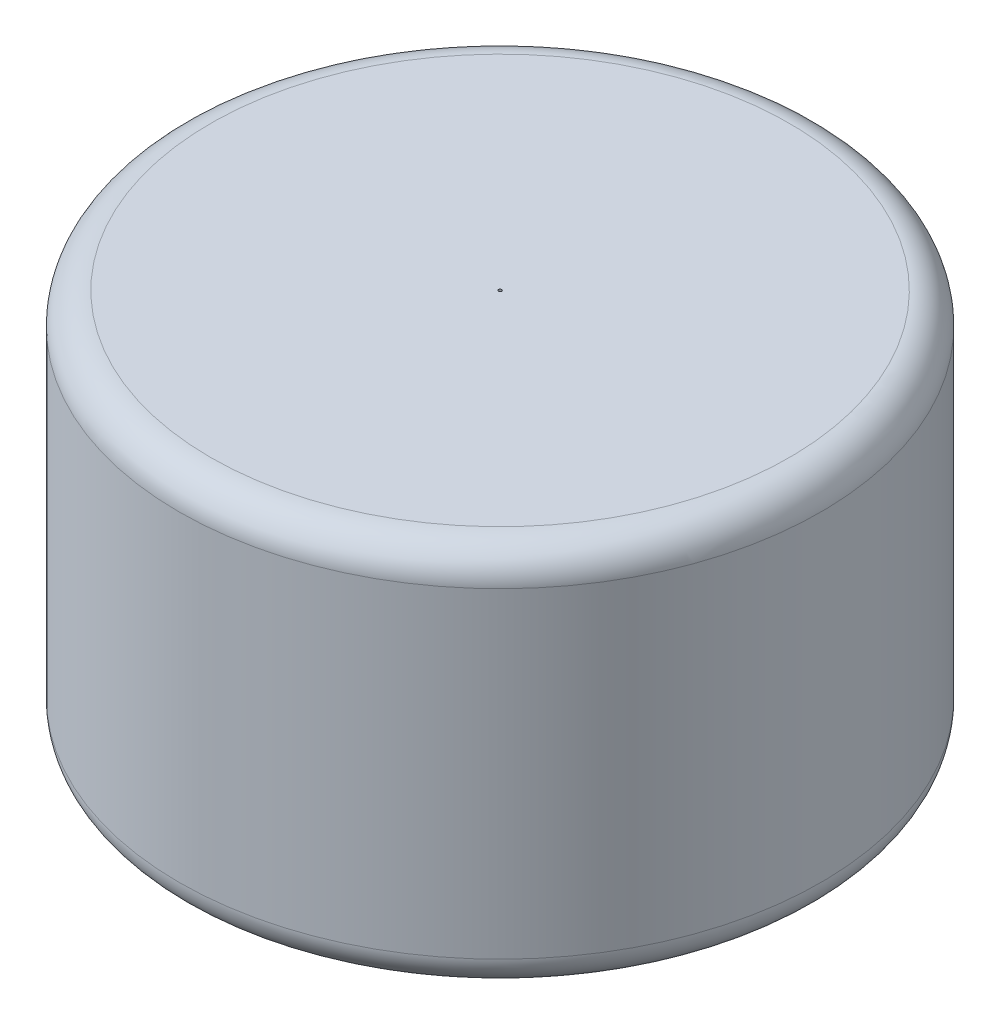
SolidWorks part; units mm, degrees
other "相机1"
other "相机2"
material "PEN"
ref_plane "前视基准面" through (0, 0, 0) normal (0, 0, 1) x (1, 0, 0)
ref_plane "上视基准面" through (0, 0, 0) normal (0, 1, 0) x (1, 0, 0)
ref_plane "右视基准面" through (0, 0, 0) normal (1, 0, 0) x (0, 0, -1)
sketch "草图1" plane through (0, 0, 0) normal (0, 1, 0) x (1, 0, 0)
  circle A0 centre (0, 0) radius 51
extrude "凸台-拉伸1" add sketch "草图1" along normal blind 61
fillet "圆角1" radius 5 2 edges at (0, 0, 51) (0, 61, 51)
sketch "草图6" plane through (0, 0, 0) normal (0, 0, 1) x (1, 0, 0)
  line L0 (0, 0) -> (0, 61)
  line L1 (46, 61) -> (-46, 61) construction
  line L2 (0, 0) -> (0, 10)
  line L4 (0, 10) -> (41, 10)
  line L5 (0, 10) -> (0, 51)
  line L6 (0, 51) -> (41, 51)
  line L7 (41, 10) -> (41, 51)
  line L8 (0, 10) -> (41, 51) construction
  line L9 (0, 51) -> (41, 10) construction
  point P9 (20.5, 30.5)
revolve "切除-旋转4" cut sketch "草图6" angle 360 about L0
sketch "草图7" plane through (0, 0, 0) normal (0, 0, 1) x (1, 0, 0)
  line L0 (46, 61) -> (-46, 61) construction
  line L1 (0, 61) -> (-0.25, 61)
  line L2 (0, 61) -> (0, 15.0221)
  line L3 (0, 15.0221) -> (-0.25, 15.0221)
  line L4 (-0.25, 61) -> (-0.25, 15.0221)
  line L5 (0, 61) -> (-0.25, 15.0221) construction
  line L6 (0, 15.0221) -> (-0.25, 61) construction
  point P4 (-0.125, 38.0111)
  point P7 (-0.125, 61)
  point P8 (0, 0)
  point P9 (0, 0)
  point P10 (0, 42.7977)
  point P11 (0, 38.8615)
  point P12 (-0.125, 27.0409)
  point P13 (0, 0)
  point P14 (0, 24.5855)
  point P15 (-0.25, -46.3889)
  point P16 (0, 0)
  point P17 (0, -42.9815)
  point P18 (0, -31.7789)
  point P19 (-0.125, 61)
  point P20 (-0.125, 61)
  point P21 (0, 8.0661)
  point P22 (0, 15.0221)
revolve "切除-旋转5" cut sketch "草图7" angle 360 about L2
